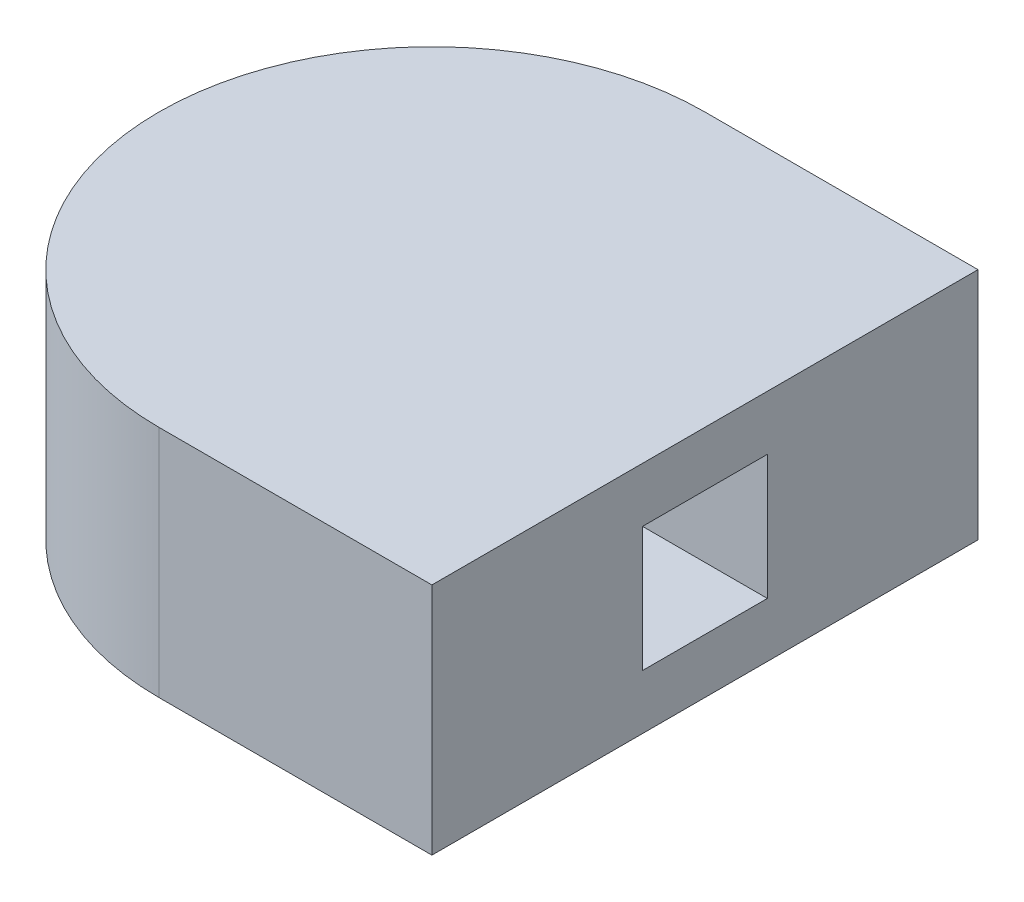
SolidWorks part; units mm, degrees
ref_plane "Front Plane" through (0, 0, 0) normal (0, 0, 1) x (1, 0, 0)
ref_plane "Top Plane" through (0, 0, 0) normal (0, 1, 0) x (1, 0, 0)
ref_plane "Right Plane" through (0, 0, 0) normal (1, 0, 0) x (0, 0, -1)
sketch "Sketch1" plane through (0, 0, 0) normal (0, 1, 0) x (1, 0, 0)
  line L1 (0, 0) -> (44.45, 0)
  line L2 (0, 0) -> (0, 44.45)
  line L3 (0, 44.45) -> (44.45, 44.45)
  line L4 (44.45, 0) -> (44.45, 44.45)
  line L5 (22.225, 44.45) -> (22.225, 0)
  arc A0 (22.225, 44.45) -> (22.225, 0) centre (22.225, 22.225) ccw
  dimension "D1" = 44.45
  dimension "D2" = 44.45
extrude "Main body extrude" add sketch "Sketch1" along normal blind 19.05 contours L5 A0 | L3 L5 L1 L4
sketch "Sketch2" plane through (44.45, 0, 0) normal (1, 0, 0) x (0, 0, -1)
  line L0 (22.225, 19.05) -> (22.225, 0) construction
  line L1 (0, 19.05) -> (44.45, 19.05) construction
  line L2 (0, 0) -> (44.45, 0) construction
  line L3 (44.45, 9.525) -> (22.225, 9.525) construction
  line L4 (44.45, 19.05) -> (44.45, 0) construction
  line L6 (17.145, 14.605) -> (27.305, 14.605)
  line L7 (17.145, 14.605) -> (17.145, 4.445)
  line L8 (17.145, 4.445) -> (27.305, 4.445)
  line L9 (27.305, 14.605) -> (27.305, 4.445)
  line L10 (17.145, 14.605) -> (27.305, 4.445) construction
  line L11 (17.145, 4.445) -> (27.305, 14.605) construction
  dimension "D1" = 10.16
  dimension "D2" = 10.16
extrude "Upper foot connection cut" cut sketch "Sketch2" against normal blind 15.24
equation "\"heelLength\"=1.75"
equation "\"D1@Sketch1\"=\"heelLength\""
equation "\"heelWidth\"=1.75"
equation "\"D2@Sketch1\"=\"heelWidth\""
equation "\"heelHeight\"=0.75"
equation "\"D1@Main body extrude\" = \"heelHeight\""
